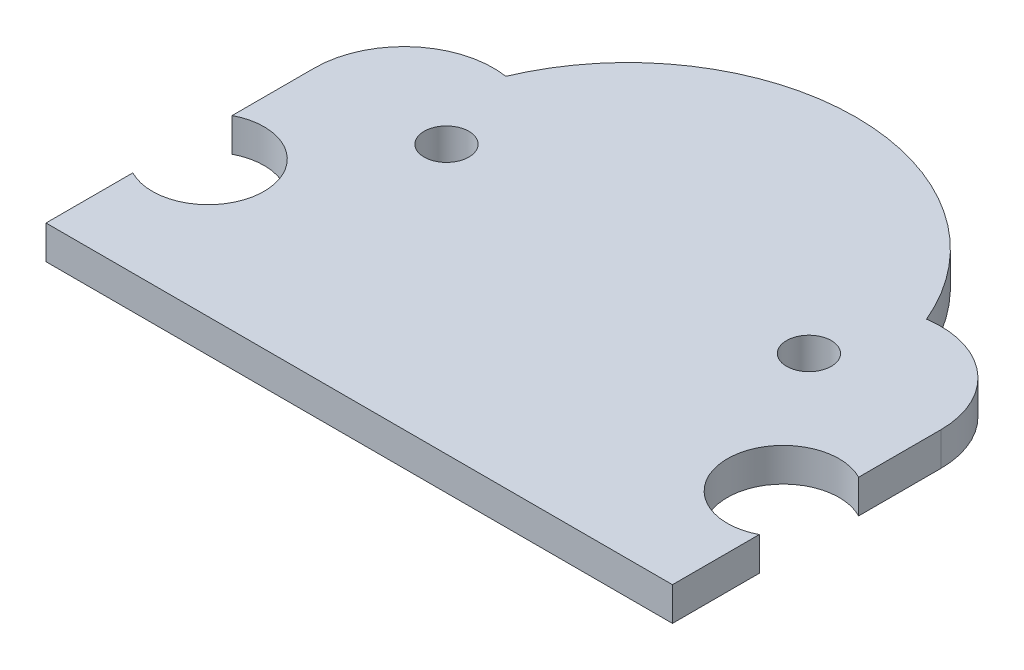
SolidWorks part; units mm, degrees
ref_plane "Front Plane" through (0, 0, 0) normal (0, 0, 1) x (1, 0, 0)
ref_plane "Top Plane" through (0, 0, 0) normal (0, 1, 0) x (1, 0, 0)
ref_plane "Right Plane" through (0, 0, 0) normal (1, 0, 0) x (0, 0, -1)
sketch "Sketch1" plane through (0, 0, 0) normal (0, 1, 0) x (1, 0, 0)
  line L0 (14, 2.2396) -> (14, -4.7282) construction
  line L1 (0, 0) -> (28, 0)
  line L20 (28, 0) -> (28, 3.8802)
  line L21 (28, 8.3198) -> (28, 12)
  line L22 (0, 12) -> (0, 8.3198)
  line L23 (0, 3.8802) -> (0, 0)
  circle A4 centre (5.9, 12) radius 1
  circle A7 centre (22.1, 12) radius 1
  arc A15 (28, 8.3198) -> (28, 3.8802) centre (26.85, 6.1) ccw
  arc A16 (28, 12) -> (23.4, 15.9547) centre (24, 12) ccw
  arc A17 (23.4, 15.9547) -> (4.6, 15.9547) centre (14, 12) ccw
  arc A18 (4.6, 15.9547) -> (0, 12) centre (4, 12) ccw
  arc A19 (0, 3.8802) -> (0, 8.3198) centre (1.15, 6.1) ccw
  point P6 (5.9, 13.1869)
  point P7 (5.9, 12)
  point P8 (0, 0)
  dimension "D1" = 10.198
  dimension "D2" = 4
  dimension "D3" = 4
  dimension "D13" = 2.5
  dimension "D14" = 2.5
  dimension "D5" = 12
  dimension "D4" = 16.2
  dimension "D11" = 2
  dimension "D6" = 25.7
  dimension "D7" = 8.1
  dimension "D8" = 12
  dimension "D9" = 3.8802
  dimension "D10" = 3.6802
  dimension "D12" = 12
  dimension "D15" = 6.1
  dimension "D16" = 28
  dimension "D17" = 28
extrude "Boss-Extrude1" add sketch "Sketch1" along normal blind 1.5
